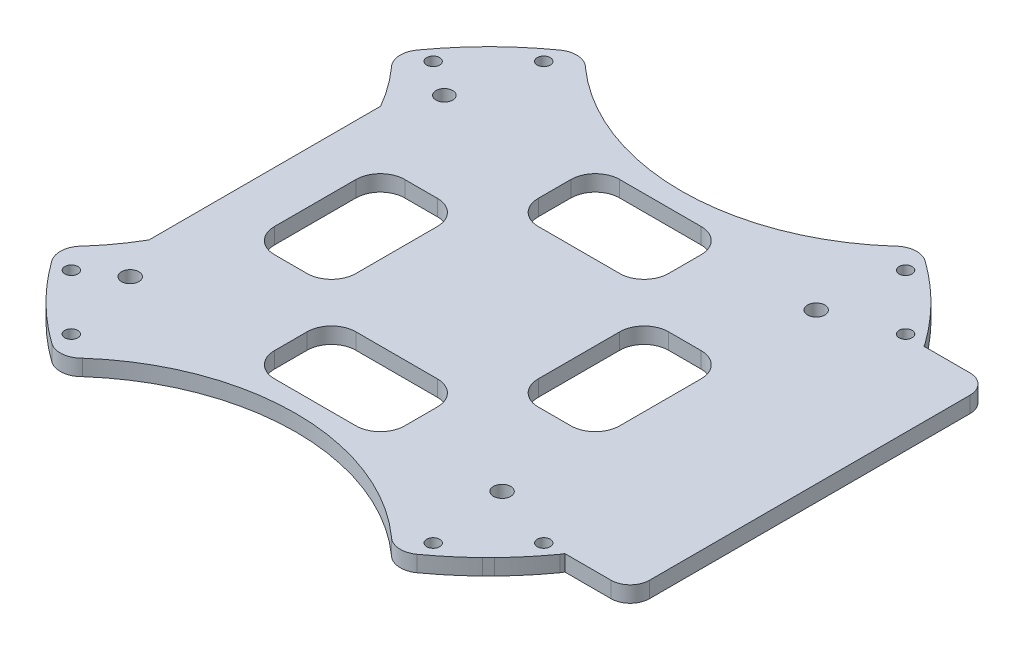
SolidWorks part; units mm, degrees
ref_plane "前视基准面" through (0, 0, 0) normal (0, 0, 1) x (1, 0, 0)
ref_plane "上视基准面" through (0, 0, 0) normal (0, 1, 0) x (1, 0, 0)
ref_plane "右视基准面" through (0, 0, 0) normal (1, 0, 0) x (0, 0, -1)
other "Configuration Table"
sketch "草图1" plane through (0, 0, 0) normal (0, 1, 0) x (1, 0, 0)
  line L8 (-39.5, -28) -> (39.5, -28) construction
  line L9 (42.5, -25) -> (42.5, 25) construction
  line L10 (39.5, 28) -> (-39.5, 28) construction
  line L11 (-42.5, 25) -> (-42.5, -25) construction
  arc A8 (-42.5, -25) -> (-39.5, -28) centre (-39.5, -25) ccw construction
  arc A9 (39.5, -28) -> (42.5, -25) centre (39.5, -25) ccw construction
  arc A10 (42.5, 25) -> (39.5, 28) centre (39.5, 25) ccw construction
  arc A11 (-39.5, 28) -> (-42.5, 25) centre (-39.5, 25) ccw construction
  circle A12 centre (19, -24.5) radius 1.35
  circle A13 centre (19, 24.5) radius 1.35
  circle A14 centre (-39, -24.5) radius 1.35
  circle A15 centre (-39, 24.5) radius 1.3
sketch "草图4" plane through (0, 0, 0) normal (0, 1, 0) x (1, 0, 0)
  line L12 (-42.4362, 34.1955) -> (-41.4914, 35.1316)
  line L13 (26.3808, 35.0047) -> (27.307, 34.0806)
  line L14 (26.4111, -34.9752) -> (27.3388, -34.048)
  line L15 (-42.7995, -33.8216) -> (-41.8783, -34.7543)
  line L16 (-42.5, 18.0646) -> (-42.5, -18.0646)
  line L17 (-42.5, 25) -> (-42.5, -25) construction
  line L18 (32.2939, 28) -> (39.5, 28)
  line L19 (39.5, 28) -> (-39.5, 28) construction
  line L20 (32.2939, -28) -> (39.5, -28)
  line L21 (-39.5, -28) -> (39.5, -28) construction
  line L22 (42.5, -25) -> (42.5, 25)
  circle A0 centre (20.5993, 36.8412) radius 1.016
  circle A1 centre (29.2204, 28.2202) radius 1.016
  circle A4 centre (29.2204, -28.2202) radius 1.016
  circle A5 centre (20.5993, -36.8412) radius 1.016
  circle A6 centre (-35.841, -36.8412) radius 1.016
  arc A8 (-41.8783, -34.7543) -> (-36.1021, -39.6265) centre (-7.6208, 0) ccw
  arc A9 (-36.1021, -39.6265) -> (-31.7262, -39.2369) centre (-34.1399, -36.8963) ccw
  arc A10 (16.4846, -39.2369) -> (-31.7262, -39.2369) centre (-7.6208, -66.2866) ccw
  arc A11 (16.4846, -39.2369) -> (20.8605, -39.6265) centre (18.8982, -36.8963) ccw
  arc A12 (20.8605, -39.6265) -> (26.4111, -34.9752) centre (-7.6208, 0) ccw
  arc A13 (27.3388, -34.048) -> (32.0056, -28.4813) centre (-7.6208, 0) ccw
  arc A14 (32.0056, -28.4813) -> (32.2939, -28) centre (29.2755, -26.519) ccw
  arc A16 (32.2939, 28) -> (32.0056, 28.4813) centre (29.2755, 26.519) ccw
  arc A17 (32.0056, 28.4813) -> (27.307, 34.0806) centre (-7.6208, 0) ccw
  arc A18 (26.3808, 35.0047) -> (20.8605, 39.6265) centre (-7.6208, 0) ccw
  arc A19 (20.8605, 39.6265) -> (16.4846, 39.2369) centre (18.8982, 36.8963) ccw
  arc A20 (-31.7262, 39.2369) -> (16.4846, 39.2369) centre (-7.6208, 66.2866) ccw
  arc A21 (-31.7262, 39.2369) -> (-36.1021, 39.6265) centre (-34.1399, 36.8963) ccw
  arc A22 (-36.1021, 39.6265) -> (-41.4914, 35.1316) centre (-7.6208, 0) ccw
  arc A23 (-42.4362, 34.1955) -> (-47.2473, 28.4813) centre (-7.6208, 0) ccw
  arc A24 (-47.2473, 28.4813) -> (-46.8578, 24.1054) centre (-44.5172, 26.519) ccw
  arc A25 (-46.8578, -24.1054) -> (-42.5, -18.0646) centre (-73.9075, 0) ccw
  arc A26 (-46.8578, -24.1054) -> (-47.2473, -28.4813) centre (-44.5172, -26.519) ccw
  arc A27 (-47.2473, -28.4813) -> (-42.7995, -33.8216) centre (-7.6208, 0) ccw
  circle A28 centre (-44.462, -28.2202) radius 1.016
  circle A30 centre (-35.841, 36.8412) radius 1.016
  circle A31 centre (-44.462, 28.2202) radius 1.016
  arc A32 (39.5, 28) -> (42.5, 25) centre (39.5, 25) cw
  arc A33 (42.5, -25) -> (39.5, -28) centre (39.5, -25) cw
  arc A34 (39.5, -28) -> (42.5, -25) centre (39.5, -25) ccw construction
  arc A35 (-42.5, 18.0646) -> (-46.8578, 24.1054) centre (-73.9075, 0) ccw
extrude "凸台-拉伸1" add sketch "草图4" along normal blind 2.5
extrude "切除-拉伸1" cut sketch "草图1" along normal up to surface (2.5 mm away) up to face at (-35.841, 2.5, -35.8252)
sketch "草图7" plane through (0, 2.5, 0) normal (0, 1, 0) x (1, 0, 0)
  line L0 (-92.4703, 0) -> (77.2286, 0) construction
  line L1 (-1.2555, -27.0415) -> (-13.9555, -27.0415)
  line L2 (2.5545, -18.1515) -> (2.5545, -23.2315)
  line L3 (-13.9555, -14.3415) -> (-1.2555, -14.3415)
  line L4 (-17.7655, -23.2315) -> (-17.7655, -18.1515)
  line L5 (6.6185, -6.4675) -> (6.6185, 6.2325)
  line L6 (15.5085, -10.2775) -> (10.4285, -10.2775)
  line L7 (19.3185, 6.2325) -> (19.3185, -6.4675)
  line L8 (10.4285, 10.0425) -> (15.5085, 10.0425)
  line L9 (-1.2555, 14.1065) -> (-13.9555, 14.1065)
  line L10 (2.5545, 22.9965) -> (2.5545, 17.9165)
  line L11 (-13.9555, 26.8065) -> (-1.2555, 26.8065)
  line L12 (-17.7655, 17.9165) -> (-17.7655, 22.9965)
  line L13 (-25.6395, -10.2775) -> (-30.7195, -10.2775)
  line L14 (-21.8295, 6.2325) -> (-21.8295, -6.4675)
  line L15 (-30.7195, 10.0425) -> (-25.6395, 10.0425)
  line L16 (-34.5295, -6.4675) -> (-34.5295, 6.2325)
  arc A0 (-1.2555, -27.0415) -> (2.5545, -23.2315) centre (-1.2555, -23.2315) ccw
  arc A1 (2.5545, -18.1515) -> (-1.2555, -14.3415) centre (-1.2555, -18.1515) ccw
  arc A2 (-13.9555, -14.3415) -> (-17.7655, -18.1515) centre (-13.9555, -18.1515) ccw
  arc A3 (6.6185, -6.4675) -> (10.4285, -10.2775) centre (10.4285, -6.4675) ccw
  arc A4 (15.5085, -10.2775) -> (19.3185, -6.4675) centre (15.5085, -6.4675) ccw
  arc A5 (19.3185, 6.2325) -> (15.5085, 10.0425) centre (15.5085, 6.2325) ccw
  arc A6 (10.4285, 10.0425) -> (6.6185, 6.2325) centre (10.4285, 6.2325) ccw
  arc A7 (-1.2555, 14.1065) -> (2.5545, 17.9165) centre (-1.2555, 17.9165) ccw
  arc A8 (2.5545, 22.9965) -> (-1.2555, 26.8065) centre (-1.2555, 22.9965) ccw
  arc A9 (-13.9555, 26.8065) -> (-17.7655, 22.9965) centre (-13.9555, 22.9965) ccw
  arc A10 (-17.7655, 17.9165) -> (-13.9555, 14.1065) centre (-13.9555, 17.9165) ccw
  arc A11 (-25.6395, -10.2775) -> (-21.8295, -6.4675) centre (-25.6395, -6.4675) ccw
  arc A12 (-21.8295, 6.2325) -> (-25.6395, 10.0425) centre (-25.6395, 6.2325) ccw
  arc A13 (-30.7195, 10.0425) -> (-34.5295, 6.2325) centre (-30.7195, 6.2325) ccw
  arc A14 (-34.5295, -6.4675) -> (-30.7195, -10.2775) centre (-30.7195, -6.4675) ccw
  arc A15 (-17.7655, -23.2315) -> (-13.9555, -27.0415) centre (-13.9555, -23.2315) ccw
  point P4 (-7.6208, 0)
extrude "切除-拉伸2" cut sketch "草图7" against normal up to surface (2.5 mm away) up to face at (19, 0, -23.15)
